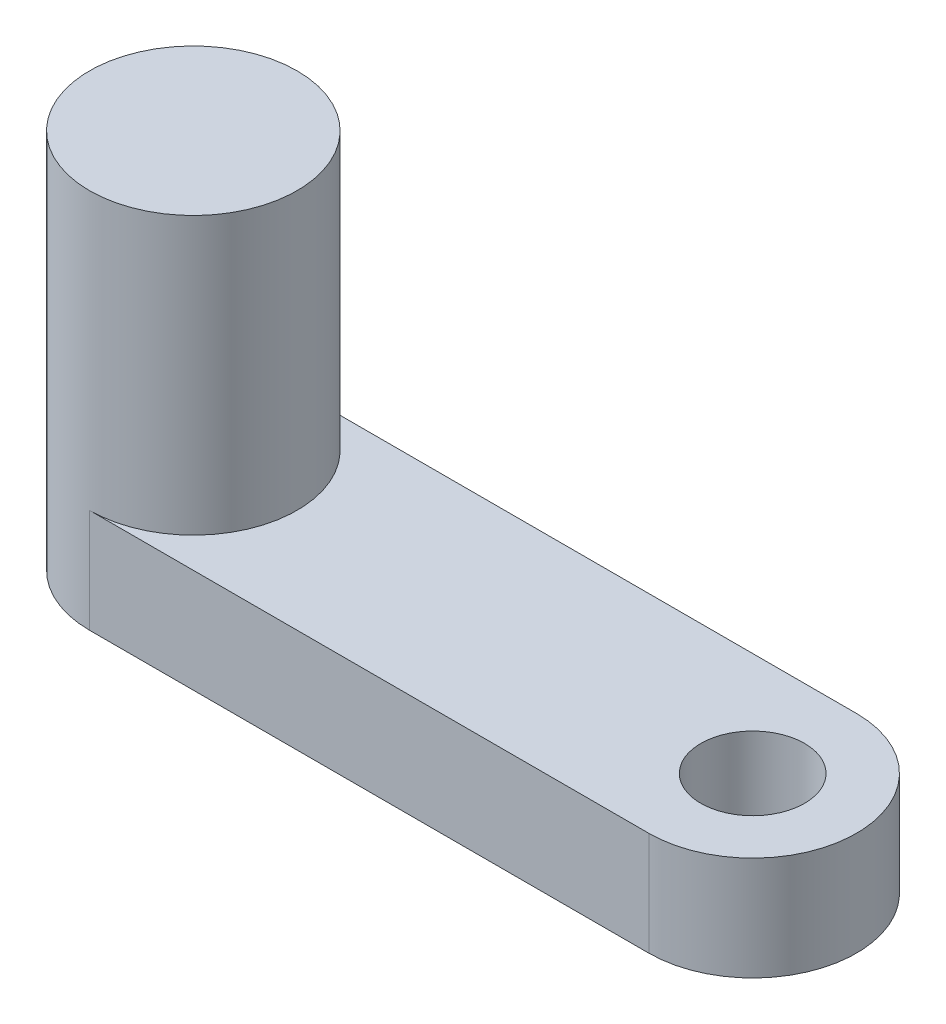
SolidWorks part; units mm, degrees
material "ABS"
ref_plane "Front Plane" through (0, 0, 0) normal (0, 0, 1) x (1, 0, 0)
ref_plane "Top Plane" through (0, 0, 0) normal (0, 1, 0) x (1, 0, 0)
ref_plane "Right Plane" through (0, 0, 0) normal (1, 0, 0) x (0, 0, -1)
sketch "Sketch1" plane through (0, 0, 0) normal (0, 1, 0) x (1, 0, 0)
  circle A0 centre (0, 0) radius 3
extrude "Boss-Extrude1" add sketch "Sketch1" along normal blind 9
sketch "Sketch2" plane through (0, 9, 0) normal (0, 1, 0) x (1, 0, 0)
  circle A0 centre (0, 0) radius 2.8
  circle A1 centre (0, 0) radius 3
  dimension "D1" = 5.6
sketch "Sketch4" plane through (0, 0, 0) normal (0, -1, 0) x (1, 0, 0)
  circle A0 centre (0, 0) radius 3
extrude "Boss-Extrude3" add sketch "Sketch4" along normal blind 2
sketch "Sketch6" plane through (0, -2, 0) normal (0, -1, 0) x (1, 0, 0)
  line L0 (0, 3) -> (16.1637, 3)
  line L1 (0, -3) -> (16.1637, -3)
  circle A0 centre (0, 0) radius 3 construction
  arc A1 (16.1637, 3) -> (16.1637, -3) centre (16.1637, 0) cw
  circle A3 centre (16.1637, 0) radius 1.5
  circle A4 centre (0, 0) radius 3 construction
  dimension "D3" = 16.1637
extrude "Boss-Extrude4" add sketch "Sketch6" against normal blind 3
sketch "Sketch7" plane through (0, -2, 0) normal (0, -1, 0) x (1, 0, 0)
  circle A0 centre (0, 0) radius 1.5
  dimension "D1" = 3
extrude "Cut-Extrude3" cut sketch "Sketch7" against normal blind 10
ref_plane "Plane1" through (0, -2, 0) normal (0, -1, 0) x (-1, 0, 0)
